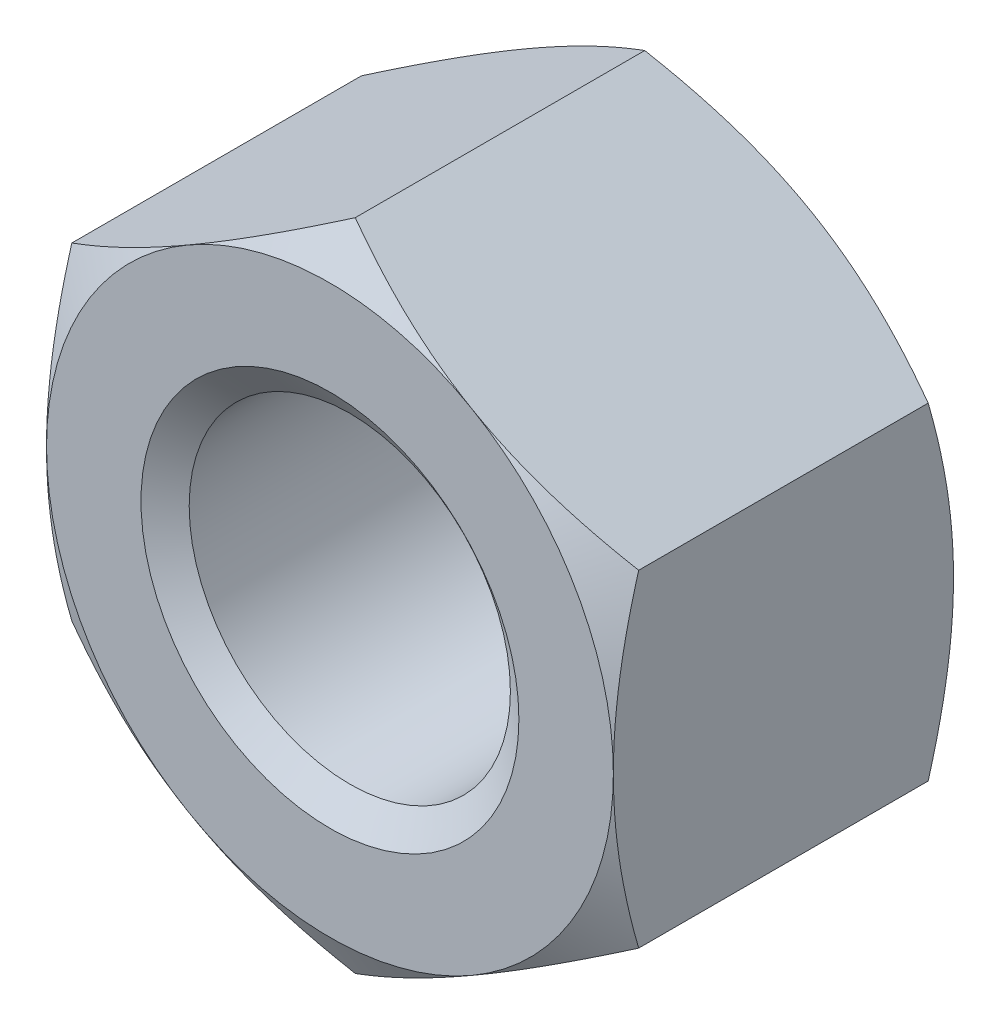
SolidWorks part; units mm, degrees
extrude "BaseNut" add sketch "BaseNutSke" against normal blind 10.8
sketch "BaseNutSke" plane through (0, 0, 0) normal (0, 0, 1) x (1, 0, 0)
  line L6 (9, 5.1962) -> (9, -5.1962)
  line L7 (-9, 5.1962) -> (-9, -5.1962)
  line L8 (9, 5.1962) -> (0, 10.3923)
  line L9 (0, 10.3923) -> (-9, 5.1962)
  line L10 (-9, -5.1962) -> (0, -10.3923)
  line L11 (0, -10.3923) -> (9, -5.1962)
  circle A0 centre (0, 0) radius 5.1
  dimension "Tap_drill" = 10.2
  dimension "Width_flats" = 18
  dimension "D2" = 9
  dimension "D3" = 9
  dimension "D1" = 120
  dimension "D4" = 9
pattern_linear "ThdSchPat" [suppressed]
revolve "ThreadSchematic" [suppressed] cut sketch "ThdSchSke" angle 360 about L6
sketch "ThdSchSke" plane through (0, 0, 0) normal (0, 1, 0) x (1, 0, 0)
  line L0 (-6, 0.0254) -> (-5.1, 0.6556)
  line L1 (-5.1, 0.6556) -> (-2.55, 0.6556)
  line L2 (-2.55, 0.6556) -> (-2.55, -0.6048)
  line L3 (-2.55, -0.6048) -> (-5.1, -0.6048)
  line L4 (-5.1, -0.6048) -> (-6, 0.0254)
  line L5 (-3.175, 1.75) -> (3.175, 1.75) construction
  line L6 (0, 1.75) -> (0, -2.9874) construction
  line L7 (0, 10.1444) -> (0, 0.6302) construction
  dimension "SideAngle" = 55
  dimension "Advance" = 1.75
  dimension "D1" = 0.0254
ref_plane "Plane1" through (0, 0, 0) normal (0, 0, 1) x (1, 0, 0)
ref_plane "Plane2" through (0, 0, 0) normal (0, 1, 0) x (1, 0, 0)
ref_plane "Plane3" through (0, 0, 0) normal (1, 0, 0) x (0, 0, -1)
sketch "Sketch4" plane through (0, 0, 0) normal (1, 0, 0) x (0, 0, -1)
  line L0 (10.8, 9) -> (10.2, 9)
  line L1 (10.8, 9) -> (10.8, 20.3923)
  line L2 (10.2, 20.3923) -> (10.8, 20.3923)
  line L3 (10.2, 20.3923) -> (10.2, 9)
  line L4 (0, 0) -> (34.925, 0) construction
  line L6 (10.8, 5.1962) -> (10.8, 10.3923) construction
  line L7 (0, 9) -> (-10, 9)
  line L8 (0, 5.1962) -> (0, 10.3923) construction
  line L9 (0.8038, 10.3923) -> (0.8038, 20.3923)
  line L10 (0.8038, 20.3923) -> (-10, 20.3923)
  line L11 (-10, 20.3923) -> (-10, 9)
  line L12 (0, 9) -> (0.8038, 10.3923)
  line L14 (0, 5.1962) -> (0, -5.1962) construction
  line L15 (10.8, 10.3923) -> (0, 10.3923) construction
  dimension "D1" = 9
  dimension "D4" = 10
  dimension "D3" = 10
  dimension "D2" = 30
revolve "Bearing-Face" [suppressed] cut sketch "Sketch4" angle 360 about L4
sketch "Sketch3" plane through (0, 0, 0) normal (1, 0, 0) x (0, 0, -1)
  line L0 (10.8, 9) -> (9.9962, 10.3923)
  line L1 (9.9962, 10.3923) -> (9.9962, 20.3923)
  line L2 (9.9962, 20.3923) -> (20.8, 20.3923)
  line L3 (20.8, 20.3923) -> (20.8, 9)
  line L4 (20.8, 9) -> (10.8, 9)
  line L5 (10.8, 5.1962) -> (10.8, 10.3923) construction
  line L6 (10.8, 10.3923) -> (0, 10.3923) construction
  line L7 (0, 0) -> (38.6776, 0) construction
  line L8 (10.8, 0) -> (0, 0) construction
  line L9 (5.4, 10.3923) -> (5.4, 44.222) construction
  line L10 (0.8038, 20.3923) -> (-10, 20.3923)
  line L11 (-10, 20.3923) -> (-10, 9)
  line L12 (-10, 9) -> (0, 9)
  line L13 (0, 9) -> (0.8038, 10.3923)
  line L14 (0.8038, 10.3923) -> (0.8038, 20.3923)
  line L16 (10.8, 10.3923) -> (0, 10.3923) construction
  dimension "D1" = 9
  dimension "D4" = 10
  dimension "D3" = 10
  dimension "D2" = 30
revolve "Double-Chamfer" cut sketch "Sketch3" angle 360 about L7
sketch "Sketch5" plane through (0, 0, 0) normal (1, 0, 0) x (0, 0, -1)
  line L0 (10.7746, 6) -> (10.0814, 5.01)
  line L1 (10.8254, 6) -> (10.7746, 6)
  line L2 (10.8254, 6) -> (10.8254, 5.01)
  line L3 (10.8254, 5.01) -> (10.0814, 5.01)
  line L6 (-0.0508, 6) -> (0, 6)
  line L7 (0, 6) -> (0.6932, 5.01)
  line L9 (0.6932, 5.01) -> (-0.0508, 5.01)
  line L10 (-0.0508, 5.01) -> (-0.0508, 6)
  line L11 (25.0375, 0) -> (38.388, 0) construction
  line L12 (10.8, 0) -> (0, 0) construction
  dimension "D1" = 35
  dimension "D2" = 0.0508
  dimension "ThreadMajor" = 6
  dimension "Offset1" = 10.8254
revolve "EndChamfer" cut sketch "Sketch5" angle 360 about L11
equation "\"D2@BaseNutSke\" = \"Width_flats@BaseNutSke\" / 2"
equation "\"D3@BaseNutSke\" = \"Width_flats@BaseNutSke\" / 2"
equation "\"D1@Sketch3\" = \"Width_flats@BaseNutSke\" /2"
equation "\"D1@Sketch4\" = \"D2@BaseNutSke\""
equation "\"D4@BaseNutSke\" = \"D3@BaseNutSke\""
equation "\"Thread_major@ThdSchSke\" = \"Thread_major@ThreadCosmetic\""
equation "\"Tap_Drill@ThdSchSke\" = \"Tap_drill@BaseNutSke\""
equation "\"OverCut@ThdSchSke\" = \"Tap_Drill@ThdSchSke\" * 0.5"
equation "\"Num_threads@ThdSchPat\" = int(  ( \"Thickness@BaseNut\" - 0.0508 ) / \"Advance@ThdSchSke\" + 0.999 )  + 1"
equation "\"Advance@ThdSchPat\" = ( \"Thickness@BaseNut\" - 0.0508 ) /  (\"Num_threads@ThdSchPat\" - 1) 'relax it"
equation "' \"Num_threads@ThdSchPat\" = \"Num_threads@ThdSchPat\" - sgn( \"Num_threads@ThdSchPat\" - 1) '---chamfered tips only---"
equation "\"ThreadMajor@Sketch5\" = \"Thread_major@ThreadCosmetic\" * 0.5"
equation "\"ChamferDepth@Sketch5\" = (\"Thread_major@ThreadCosmetic\" - \"Tap_drill@BaseNutSke\") * 0.55"
equation "\"Offset1@Sketch5\" = \"Thickness@BaseNut\" + 0.0254"
equation "\"Offset2@Sketch5\" = \"Offset1@Sketch5\" + 0.0508"
